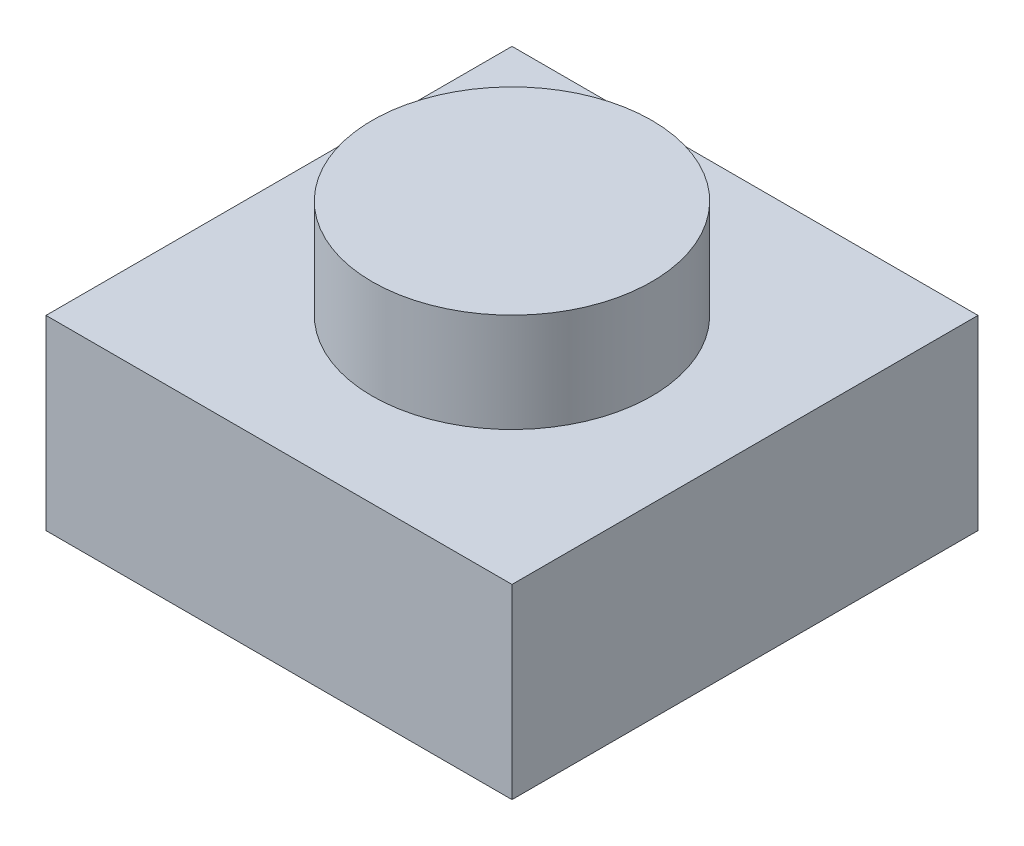
SolidWorks part; units mm, degrees
ref_plane "前基準面" through (0, 0, 0) normal (0, 0, 1) x (1, 0, 0)
ref_plane "上基準面" through (0, 0, 0) normal (0, 1, 0) x (1, 0, 0)
ref_plane "右基準面" through (0, 0, 0) normal (1, 0, 0) x (0, 0, -1)
sketch "草圖1" plane through (0, 0, 0) normal (0, 1, 0) x (1, 0, 0)
  line L1 (-4, -4) -> (4, -4)
  line L2 (-4, -4) -> (-4, 4)
  line L3 (-4, 4) -> (4, 4)
  line L4 (4, -4) -> (4, 4)
  line L5 (-4, -4) -> (4, 4) construction
  line L6 (-4, 4) -> (4, -4) construction
  point P0 (0, 0)
  dimension "width" = 8
  dimension "length" = 8
extrude "height" add sketch "草圖1" along normal blind 3.2
sketch "草圖2" plane through (0, 3.2, 0) normal (0, 1, 0) x (1, 0, 0)
  circle A0 centre (0, 0) radius 2.4
  dimension "D1" = 4.8
extrude "填料-伸長2" add sketch "草圖2" along normal blind 1.7
shell "薄殼1" thickness 1.6
